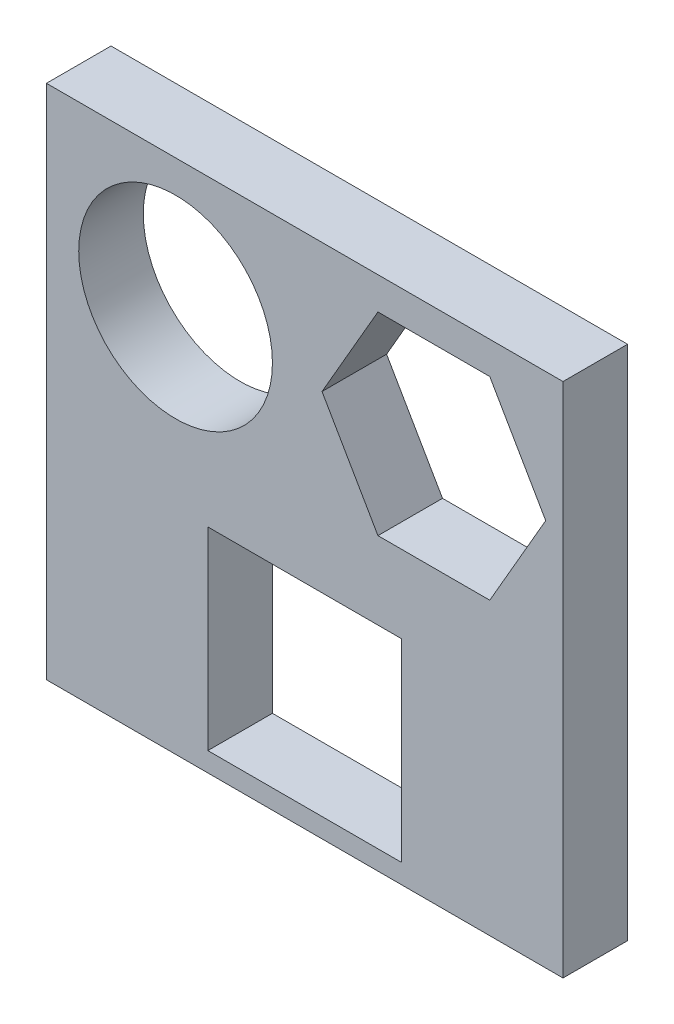
SolidWorks part; units mm, degrees
ref_plane "Front Plane" through (0, 0, 0) normal (0, 0, 1) x (1, 0, 0)
ref_plane "Top Plane" through (0, 0, 0) normal (0, 1, 0) x (1, 0, 0)
ref_plane "Right Plane" through (0, 0, 0) normal (1, 0, 0) x (0, 0, -1)
sketch "Sketch1" plane through (0, 0, 0) normal (0, 0, 1) x (1, 0, 0)
  line L1 (-40, -40) -> (40, -40)
  line L2 (-40, -40) -> (-40, 40)
  line L3 (-40, 40) -> (40, 40)
  line L4 (40, -40) -> (40, 40)
  line L5 (-40, -40) -> (40, 40) construction
  line L6 (-40, 40) -> (40, -40) construction
  line L7 (11.3397, 35) -> (2.6795, 20)
  line L8 (2.6795, 20) -> (11.3397, 5)
  line L9 (11.3397, 5) -> (28.6603, 5)
  line L10 (28.6603, 5) -> (37.3205, 20)
  line L11 (37.3205, 20) -> (28.6603, 35)
  line L12 (28.6603, 35) -> (11.3397, 35)
  line L13 (-15, -7) -> (15, -7)
  line L14 (-15, -7) -> (-15, -37)
  line L15 (-15, -37) -> (15, -37)
  line L16 (15, -7) -> (15, -37)
  line L17 (-15, -7) -> (15, -37) construction
  line L18 (-15, -37) -> (15, -7) construction
  circle A0 centre (-20, 20) radius 15
  circle A1 centre (20, 20) radius 15 construction
  point P0 (0, 0)
  point P8 (0, -22)
  dimension "D3" = 30
  dimension "D4" = 30
  dimension "D1" = 80
  dimension "D2" = 80
  dimension "D5" = 20
  dimension "D6" = 20
  dimension "D7" = 30
  dimension "D8" = 30
  dimension "D9" = 18
  dimension "D10" = 40
extrude "Boss-Extrude1" add sketch "Sketch1" against normal blind 10
